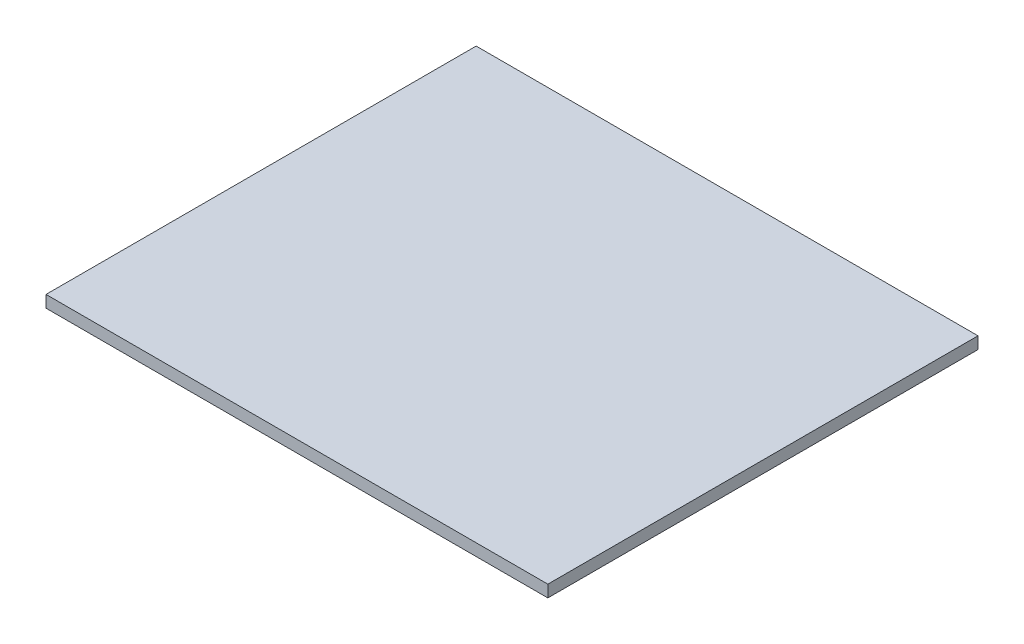
SolidWorks part; units mm, degrees
ref_plane "Front Plane" through (0, 0, 0) normal (0, 0, 1) x (1, 0, 0)
ref_plane "Top Plane" through (0, 0, 0) normal (0, 1, 0) x (1, 0, 0)
ref_plane "Right Plane" through (0, 0, 0) normal (1, 0, 0) x (0, 0, -1)
sketch "Sketch1" plane through (0, 0, 0) normal (0, 1, 0) x (1, 0, 0)
  line L1 (-133.35, 114.3) -> (133.35, 114.3)
  line L2 (-133.35, 114.3) -> (-133.35, -114.3)
  line L3 (-133.35, -114.3) -> (133.35, -114.3)
  line L4 (133.35, 114.3) -> (133.35, -114.3)
  line L5 (-133.35, 114.3) -> (133.35, -114.3) construction
  line L6 (-133.35, -114.3) -> (133.35, 114.3) construction
  point P0 (0, 0)
  dimension "D1" = 266.7
  dimension "D2" = 228.6
extrude "Boss-Extrude1" add sketch "Sketch1" along normal mid plane 6.35 contours L1 L4 L3 L2
